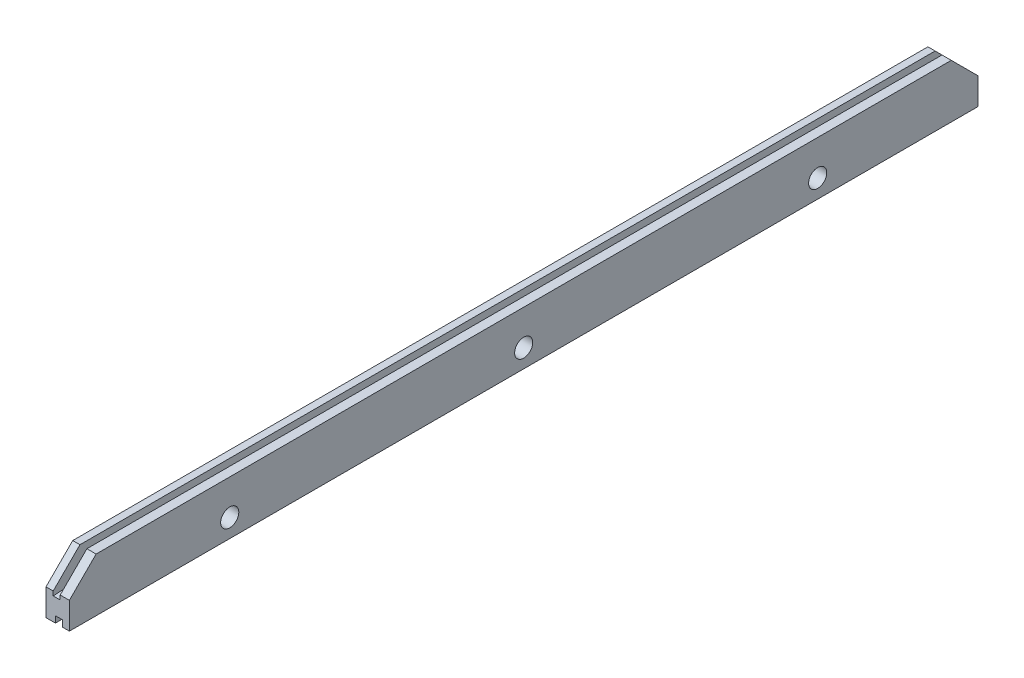
SolidWorks part; units mm, degrees
material "Delrin 2700 NC010, Low Viscosity Acetal Copolymer (SS)"
ref_plane "Front Plane" through (0, 0, 0) normal (0, 0, 1) x (1, 0, 0)
ref_plane "Top Plane" through (0, 0, 0) normal (0, 1, 0) x (1, 0, 0)
ref_plane "Right Plane" through (0, 0, 0) normal (1, 0, 0) x (0, 0, -1)
sketch "Sketch1" plane through (0, 0, 0) normal (0, 0, 1) x (1, 0, 0)
  line L0 (0, 4.7625) -> (0, -4.7625)
  line L1 (0, -13.2224) -> (0, 13.2224) construction
  line L4 (0, -4.7625) -> (5.5562, -4.7625)
  line L5 (5.5562, -4.7625) -> (5.5562, 4.7625)
  line L6 (5.5562, 4.7625) -> (0, 4.7625)
  point P11 (0, 0)
  dimension "D5" = 5.5562
  dimension "D7" = 9.525
extrude "Boss-Extrude1" add sketch "Sketch1" along normal mid plane 215.9
sketch "Sketch17" plane through (0, 0, 107.95) normal (0, 0, 1) x (1, 0, 0)
  line L0 (5.5562, 4.7625) -> (0, 4.7625) construction
  line L1 (1.7145, 4.7625) -> (3.3655, 4.7625)
  line L2 (1.7145, 4.7625) -> (1.7145, 2.0955)
  line L3 (1.7145, 2.0955) -> (3.3655, 2.0955)
  line L4 (3.3655, 4.7625) -> (3.3655, 2.0955)
  line L5 (0, 4.7625) -> (0, -4.7625) construction
  dimension "D1" = 1.7145
  dimension "D2" = 2.667
  dimension "D3" = 1.651
extrude "Cut-Extrude8" cut sketch "Sketch17" against normal through all
sketch "Sketch18" plane through (0, 0, 107.95) normal (0, 0, 1) x (1, 0, 0)
  line L1 (2.2352, -4.7625) -> (3.8862, -4.7625)
  line L2 (2.2352, -4.7625) -> (2.2352, -3.2385)
  line L3 (2.2352, -3.2385) -> (3.8862, -3.2385)
  line L4 (3.8862, -4.7625) -> (3.8862, -3.2385)
  line L5 (0, -4.7625) -> (5.5562, -4.7625) construction
  line L6 (0, 4.7625) -> (0, -4.7625) construction
  dimension "D1" = 2.2352
  dimension "D2" = 1.651
  dimension "D3" = 1.524
extrude "Cut-Extrude9" cut sketch "Sketch18" against normal through all
hole_wizard "M2.5 Clearance Hole1" [suppressed] positions "Sketch19" profile "Sketch20" hole size "M2.5" standard "ANSI Metric"
sketch "Sketch19" plane through (4.7625, 0, 0) normal (1, 0, 0) x (0, 0, -1)
  line L0 (0, 2.6194) -> (0, -2.6194) construction
  line L1 (-25.4, 4.7625) -> (25.4, 4.7625) construction
  point P0 (0, 1.5875)
  dimension "D1" = 3.175
sketch "Sketch20" plane through (4.7625, 1.5875, 0) normal (0, 1, 0) x (0, 0, -1)
  line L0 (0, 0) -> (0, 4.7625)
  line L1 (0, 4.7625) -> (1.45, 4.7625)
  line L2 (1.45, 4.7625) -> (1.45, 0)
  line L5 (1.45, 0) -> (0, 0)
  line L11 (0, -6.35) -> (0, 107.95) construction
  dimension "Thru Hole Dia." = 2.9
  dimension "Thru Hole Depth" = 4.7625
sketch "Sketch21" [suppressed] plane through (4.7625, 0, 0) normal (1, 0, 0) x (0, 0, -1)
  line L0 (-4.3656, 1.5875) -> (-4.3656, 4.7625)
  line L1 (-25.4, 4.7625) -> (25.4, 4.7625) construction
  line L2 (-4.3656, 4.7625) -> (4.3656, 4.7625)
  line L3 (4.3656, 4.7625) -> (4.3656, 1.5875)
  arc A0 (-4.3656, 1.5875) -> (4.3656, 1.5875) centre (0, 1.5875) ccw
  dimension "D1" = 8.7312
extrude "Cut-Extrude11" [suppressed] cut sketch "Sketch21" against normal blind 2.54
pattern_linear "LPattern1" [suppressed] count 2 spacing 63.5
hole_wizard "#18 (0.1695) Diameter Hole1" positions "Sketch22" profile "Sketch23" hole size "#18" standard "ANSI Inch" end condition through all
sketch "Sketch22" plane through (0, 0, 0) normal (-1, 0, 0) x (0, 0, 1)
  line L0 (0, -3.0559) -> (0, 3.0559) construction
  line L1 (107.95, -4.7625) -> (-107.95, -4.7625) construction
  point P0 (69.85, -0.3969)
  point P2 (-69.85, -0.3969)
  point P9 (0, -0.3969)
  dimension "D1" = 69.85
  dimension "D2" = 69.85
  dimension "D3" = 4.3656
sketch "Sketch23" plane through (0, -0.3969, 69.85) normal (0, 1, 0) x (0, 0, 1)
  line L0 (0, 0) -> (0, 5.5562)
  line L1 (0, 5.5562) -> (2.1526, 5.5562)
  line L2 (2.1526, 5.5562) -> (2.1526, 0)
  line L5 (2.1526, 0) -> (0, 0)
  line L11 (0, -6.35) -> (0, 107.95) construction
  dimension "Thru Hole Dia." = 4.3053
  dimension "Thru Hole Depth" = 5.5562
sketch "Sketch24" plane through (0, 0, 107.95) normal (0, 0, 1) x (1, 0, 0)
  line L0 (5.5562, -4.7625) -> (5.5562, 4.7625) construction
  line L1 (0, 4.7625) -> (5.5562, 4.7625)
  line L2 (0, 4.7625) -> (0, 2.0955)
  line L3 (0, 2.0955) -> (5.5562, 2.0955)
  line L4 (5.5562, 4.7625) -> (5.5562, 2.0955)
  line L5 (1.7145, 2.0955) -> (3.3655, 2.0955) construction
extrude "Cut-Extrude12" [suppressed] cut sketch "Sketch24" against normal through all
chamfer "Chamfer1" distance 1.524 distance2 25.4 1 edges at (2.54, 2.0955, 107.95)
chamfer "Chamfer2" distance 25.4 distance2 1.524 1 edges at (2.54, 2.0955, -107.95)
sketch "Sketch25" plane through (0, 4.7625, 0) normal (0, 1, 0) x (1, 0, 0)
  line L4 (0, -107.95) -> (1.7145, -107.95)
  line L5 (1.7145, -107.95) -> (1.7145, 107.95)
  line L6 (1.7145, 107.95) -> (0, 107.95)
  line L7 (0, 107.95) -> (0, -107.95)
  line L8 (0, -107.95) -> (1.7145, -107.95)
  line L9 (1.7145, -107.95) -> (1.7145, 107.95)
  line L10 (1.7145, 107.95) -> (0, 107.95)
  line L11 (0, 107.95) -> (0, -107.95)
  line L12 (5.5562, 107.95) -> (3.3655, 107.95)
  line L13 (3.3655, 107.95) -> (3.3655, -107.95)
  line L14 (3.3655, -107.95) -> (5.5562, -107.95)
  line L15 (5.5562, -107.95) -> (5.5562, 107.95)
  line L16 (5.5562, 107.95) -> (3.3655, 107.95)
  line L17 (3.3655, 107.95) -> (3.3655, -107.95)
  line L18 (3.3655, -107.95) -> (5.5562, -107.95)
  line L19 (5.5562, -107.95) -> (5.5562, 107.95)
  dimension "D1" = 0
  dimension "D2" = 0
extrude "Boss-Extrude2" add sketch "Sketch25" along normal blind 3.175
chamfer "Chamfer3" distance 6.35 angle 45 4 edges at (0.8572, 7.9375, -107.95) (4.4609, 7.9375, -107.95) (0.8572, 7.9375, 107.95) (4.4609, 7.9375, 107.95)
